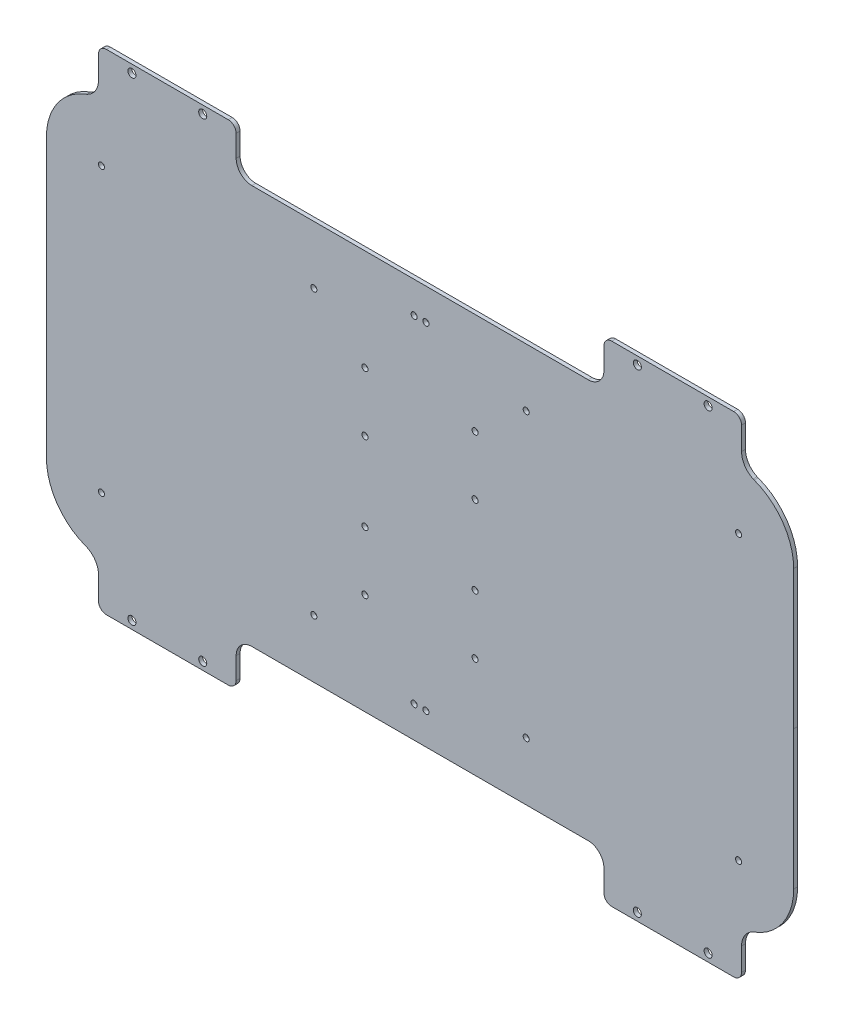
SolidWorks part; units mm, degrees
material "Thornel Mat VMA"
ref_plane "Front Plane" through (0, 0, 0) normal (0, 0, 1) x (1, 0, 0)
ref_plane "Top Plane" through (0, 0, 0) normal (0, 1, 0) x (1, 0, 0)
ref_plane "Right Plane" through (0, 0, 0) normal (1, 0, 0) x (0, 0, -1)
sketch "Sketch1" plane through (0, 0, 0) normal (0, 0, 1) x (1, 0, 0)
  line L0 (-89.5, -124.5) -> (-89.5, -101.5)
  line L1 (0, 0) -> (-188.8511, 0) construction
  line L2 (0, 0) -> (0, -155.176) construction
  line L4 (-167.5, -124.5) -> (-89.5, -124.5)
  line L15 (-167.5, -124.5) -> (-167.5, 124.5)
  line L16 (0, -153.8218) -> (0, 153.8218) construction
  line L17 (0, 0) -> (239.2725, 0) construction
  line L18 (-89.5, -113) -> (-167.5, -113) construction
  line L23 (-128.5, -113) -> (-128.5, -112.4029) construction
  line L24 (-146.5, -120.5) -> (-110.5, -120.5) construction
  line L29 (-128.5, -120.5) -> (-128.5, -79.0973) construction
  line L30 (128.5, -120.5) -> (128.5, -79.0973) construction
  line L35 (146.5, -120.5) -> (110.5, -120.5) construction
  line L36 (128.5, -113) -> (128.5, -112.4029) construction
  line L41 (89.5, -113) -> (167.5, -113) construction
  line L42 (167.5, -124.5) -> (167.5, 124.5)
  line L49 (167.5, -124.5) -> (89.5, -124.5)
  line L72 (89.5, -124.5) -> (89.5, -101.5)
  line L77 (89.5, 113) -> (167.5, 113) construction
  line L83 (128.5, 113) -> (128.5, 112.4029) construction
  line L84 (146.5, 120.5) -> (110.5, 120.5) construction
  line L89 (128.5, 120.5) -> (128.5, 79.0973) construction
  line L90 (-128.5, 120.5) -> (-128.5, 79.0973) construction
  line L95 (-146.5, 120.5) -> (-110.5, 120.5) construction
  line L96 (-128.5, 113) -> (-128.5, 112.4029) construction
  line L101 (-89.5, 113) -> (-167.5, 113) construction
  line L102 (89.5, 101.5) -> (-89.5, 101.5)
  line L108 (89.5, -101.5) -> (-89.5, -101.5)
  line L109 (89.5, 124.5) -> (89.5, 101.5)
  line L110 (167.5, 124.5) -> (89.5, 124.5)
  line L113 (-167.5, 124.5) -> (-89.5, 124.5)
  line L114 (-89.5, 124.5) -> (-89.5, 101.5)
  circle A2 centre (-146.5, -120.5) radius 2.05
  circle A3 centre (-110.5, -120.5) radius 2.05
  circle A4 centre (146.5, -120.5) radius 2.05
  circle A5 centre (110.5, -120.5) radius 2.05
  circle A42 centre (110.5, -120.5) radius 2.05
  circle A43 centre (146.5, -120.5) radius 2.05
  circle A44 centre (146.5, 120.5) radius 2.05
  circle A45 centre (110.5, 120.5) radius 2.05
  circle A48 centre (110.5, 120.5) radius 2.05
  circle A49 centre (146.5, 120.5) radius 2.05
  circle A50 centre (-110.5, 120.5) radius 2.05
  circle A51 centre (-146.5, 120.5) radius 2.05
  circle A52 centre (-28, -50) radius 1.55
  circle A53 centre (-28, -20) radius 1.55
  circle A54 centre (-28, 20) radius 1.55
  circle A55 centre (-28, 50) radius 1.55
  circle A56 centre (28, 50) radius 1.55
  circle A57 centre (28, 20) radius 1.55
  circle A58 centre (28, -20) radius 1.55
  circle A59 centre (28, -50) radius 1.55
  circle A109 centre (-162, -72) radius 1.55
  circle A110 centre (-54, -72) radius 1.55
  circle A111 centre (-162, 72) radius 1.55
  circle A112 centre (-54, 72) radius 1.55
  circle A113 centre (162, 72) radius 1.55
  circle A114 centre (54, 72) radius 1.55
  circle A115 centre (162, -72) radius 1.55
  circle A116 centre (54, -72) radius 1.55
  point P24 (0, -101.5)
  point P69 (167.5, 0)
  point P70 (-167.5, 0)
  point P71 (0, 101.5)
  dimension "D6" = 4
  dimension "D10" = 108
  dimension "D16" = 3.1
  dimension "D4" = 36
  dimension "D5" = 4.1
  dimension "D7" = 78
  dimension "D9" = 54
  dimension "D11" = 72
  dimension "D14" = 30
  dimension "D15" = 40
  dimension "D17" = 56
  dimension "D2" = 3.1
  dimension "D1" = 249
  dimension "D3" = 23
  dimension "D8" = 335
extrude "Boss-Extrude1" add sketch "Sketch1" along normal blind 2
fillet "圆角1" radius 10 4 edges at (-89.5, 101.5, 1) (89.5, 101.5, 1) (89.5, -101.5, 1) (-89.5, -101.5, 1)
fillet "圆角2" radius 3 8 edges at (167.5, -124.5, 1) (167.5, 124.5, 1) (-167.5, -124.5, 1) (-167.5, 124.5, 1) (89.5, 124.5, 1) (-89.5, 124.5, 1) (89.5, -124.5, 1) (-89.5, -124.5, 1)
sketch "草图1" plane through (0, 0, 2) normal (0, 0, 1) x (1, 0, 0)
  line L1 (0, 0) -> (-225.2559, 0) construction
  line L2 (0, 0) -> (0, -150.0532) construction
  line L3 (-189.9974, 0) -> (-190, -70.5859)
  line L4 (-165.4164, -103.8012) -> (-165.4164, 0)
  line L5 (-165.4164, 103.8012) -> (-165.4164, 0)
  line L6 (-189.9974, 0) -> (-190, 70.5859)
  line L7 (189.9974, 0) -> (190, 70.5859)
  line L8 (165.4164, 103.8012) -> (165.4164, 0)
  line L9 (165.4164, -103.8012) -> (165.4164, 0)
  line L10 (189.9974, 0) -> (190, -70.5859)
  arc A2 (-190, 70.5859) -> (-169.9278, 99.5417) centre (-159.0801, 70.5871) cw
  arc A3 (-169.9278, -99.5417) -> (-165.4164, -103.8012) centre (-172.7345, -107.0332) cw
  arc A4 (-190, -70.5859) -> (-169.9278, -99.5417) centre (-159.0801, -70.5871) ccw
  arc A5 (-169.9278, 99.5417) -> (-165.4164, 103.8012) centre (-172.7345, 107.0332) ccw
  arc A6 (169.9278, 99.5417) -> (165.4164, 103.8012) centre (172.7345, 107.0332) cw
  arc A7 (190, -70.5859) -> (169.9278, -99.5417) centre (159.0801, -70.5871) cw
  arc A8 (169.9278, -99.5417) -> (165.4164, -103.8012) centre (172.7345, -107.0332) ccw
  arc A9 (190, 70.5859) -> (169.9278, 99.5417) centre (159.0801, 70.5871) ccw
  dimension "D1" = 8
extrude "凸台-拉伸1" add sketch "草图1" against normal up to surface (2 mm away) contours L7 A9 A6 L8 L9 A8 A7 L10 | L5 L4 A3 A4 L3 L6 A2 A5 up to face at (163.55, -72, 0)
sketch "草图2" plane through (0, 0, 0) normal (0, 0, -1) x (-1, 0, 0)
  line L0 (-163.5, 108.8821) -> (-163.5, 125.1276)
  line L2 (-110.5, 120.5) -> (-146.5, 120.5) construction
  line L4 (-128.5, 120.5) -> (-128.5, 139.8938) construction
  line L5 (-163.5, 125.1276) -> (-195.49, 125.1276)
  line L6 (-195.49, 125.1276) -> (-190, 70.5859)
  line L7 (-60.8067, 101.5) -> (-85.5, 101.5)
  line L8 (-79.5, 101.5) -> (79.5, 101.5) construction
  line L9 (-93.5, 109.5) -> (-93.5, 125.1276)
  line L10 (-93.5, 125.1276) -> (-60.8067, 125.1276)
  line L11 (-60.8067, 125.1276) -> (-60.8067, 101.5)
  line L12 (0, 0) -> (0, -176.2697) construction
  line L13 (0, 0) -> (232.0428, 0) construction
  line L14 (128.5, 120.5) -> (128.5, 139.8938) construction
  line L15 (110.5, 120.5) -> (146.5, 120.5) construction
  line L16 (60.8067, 125.1276) -> (60.8067, 101.5)
  line L17 (93.5, 125.1276) -> (60.8067, 125.1276)
  line L18 (93.5, 109.5) -> (93.5, 125.1276)
  line L19 (60.8067, 101.5) -> (85.5, 101.5)
  line L20 (195.49, 125.1276) -> (190, 70.5859)
  line L21 (163.5, 125.1276) -> (195.49, 125.1276)
  line L22 (163.5, 108.8821) -> (163.5, 125.1276)
  line L23 (110.5, -120.5) -> (146.5, -120.5) construction
  line L24 (128.5, -120.5) -> (128.5, -139.8938) construction
  line L25 (-128.5, -120.5) -> (-128.5, -139.8938) construction
  line L26 (-110.5, -120.5) -> (-146.5, -120.5) construction
  line L27 (163.5, -108.8821) -> (163.5, -125.1276)
  line L28 (163.5, -125.1276) -> (195.49, -125.1276)
  line L29 (195.49, -125.1276) -> (190, -70.5859)
  line L30 (60.8067, -101.5) -> (85.5, -101.5)
  line L31 (93.5, -109.5) -> (93.5, -125.1276)
  line L32 (93.5, -125.1276) -> (60.8067, -125.1276)
  line L33 (60.8067, -125.1276) -> (60.8067, -101.5)
  line L34 (-60.8067, -125.1276) -> (-60.8067, -101.5)
  line L35 (-93.5, -125.1276) -> (-60.8067, -125.1276)
  line L36 (-93.5, -109.5) -> (-93.5, -125.1276)
  line L37 (-60.8067, -101.5) -> (-85.5, -101.5)
  line L38 (-195.49, -125.1276) -> (-190, -70.5859)
  line L39 (-163.5, -125.1276) -> (-195.49, -125.1276)
  line L40 (-163.5, -108.8821) -> (-163.5, -125.1276)
  arc A0 (-169.9278, 99.5417) -> (-190, 70.5859) centre (-159.0801, 70.5871) ccw construction
  arc A1 (-169.9761, 99.5235) -> (-190, 70.5859) centre (-159.0801, 70.5871) ccw
  arc A2 (-169.9761, 99.5235) -> (-163.5, 108.8821) centre (-173.5, 108.8821) ccw
  arc A3 (-85.5, 101.5) -> (-93.5, 109.5) centre (-85.5, 109.5) cw
  arc A4 (85.5, 101.5) -> (93.5, 109.5) centre (85.5, 109.5) ccw
  arc A5 (169.9761, 99.5235) -> (163.5, 108.8821) centre (173.5, 108.8821) cw
  arc A6 (169.9761, 99.5235) -> (190, 70.5859) centre (159.0801, 70.5871) cw
  arc A7 (169.9761, -99.5235) -> (190, -70.5859) centre (159.0801, -70.5871) ccw
  arc A8 (169.9761, -99.5235) -> (163.5, -108.8821) centre (173.5, -108.8821) ccw
  arc A9 (85.5, -101.5) -> (93.5, -109.5) centre (85.5, -109.5) cw
  arc A10 (-85.5, -101.5) -> (-93.5, -109.5) centre (-85.5, -109.5) ccw
  arc A11 (-169.9761, -99.5235) -> (-163.5, -108.8821) centre (-173.5, -108.8821) cw
  arc A12 (-169.9761, -99.5235) -> (-190, -70.5859) centre (-159.0801, -70.5871) cw
  dimension "D2" = 10
  dimension "D3" = 8
  dimension "D1" = 35
extrude "切除-拉伸1" cut sketch "草图2" against normal blind 10
fillet "圆角3" radius 4 8 edges at (-93.5, 124.5, 1) (-163.5, 124.5, 1) (93.5, 124.5, 1) (163.5, 124.5, 1) (163.5, -124.5, 1) (93.5, -124.5, 1) (-93.5, -124.5, 1) (-163.5, -124.5, 1)
sketch "Sketch2" plane through (0, 0, 0) normal (0, 0, -1) x (-1, 0, 0)
  line L0 (-22.86, 27.4315) -> (22.86, 27.4332) construction
  line L2 (0, 27.4324) -> (0, -47.4376) construction
  line L3 (0, -47.4376) -> (-24.13, -47.4376) construction
  line L4 (-24.13, -47.4376) -> (-24.13, -48.7376) construction
  line L5 (-24.13, -48.7376) -> (24.13, -48.7376) construction
  circle A0 centre (22.86, 27.4332) radius 1.55
  circle A1 centre (-22.86, 27.4315) radius 1.55
  circle A2 centre (-24.13, -47.4376) radius 1.55
  circle A3 centre (24.13, -48.7376) radius 1.55
  circle A4 centre (1.21, 13.4615) radius 1.55
  point P0 (0, -10.0026)
  point P3 (0, 27.4324)
  dimension "D1" = 3.1
  dimension "D2" = 45.72
  dimension "D3" = 74.87
  dimension "D4" = 24.13
  dimension "D5" = 1.3
  dimension "D6" = 48.26
  dimension "D7" = 24.07
  dimension "D8" = 13.97
  dimension "D9" = 10.0026
sketch "Sketch3" plane through (0, 0, 0) normal (0, 0, -1) x (-1, 0, 0)
  line L1 (-82, -52.5) -> (-82, 52.5) construction
  line L2 (-82, -52.5) -> (-58, -52.5) construction
  line L3 (-58, -52.5) -> (-58, 52.5) construction
  line L4 (-82, 52.5) -> (-58, 52.5) construction
  line L5 (-82, -52.5) -> (-58, 52.5) construction
  line L6 (-58, -52.5) -> (-82, 52.5) construction
  circle A0 centre (-58, 52.5) radius 1.55
  circle A1 centre (-82, 52.5) radius 1.55
  circle A2 centre (-58, -52.5) radius 1.55
  circle A3 centre (-82, -52.5) radius 1.55
  point P0 (-70, 0)
  dimension "D1" = 3.1
  dimension "D2" = 105
  dimension "D3" = 24
  dimension "D4" = 70
sketch "Sketch4" plane through (0, 0, 0) normal (0, 0, -1) x (-1, 0, 0)
  line L0 (190, -70.5859) -> (189.9974, 0) construction
  line L1 (51.9974, 36) -> (87.9974, 36) construction
  line L2 (51.9974, 36) -> (51.9974, -36) construction
  line L3 (51.9974, -36) -> (87.9974, -36) construction
  line L4 (87.9974, 36) -> (87.9974, -36) construction
  line L5 (51.9974, 36) -> (87.9974, -36) construction
  line L6 (51.9974, -36) -> (87.9974, 36) construction
  circle A0 centre (51.9974, -36) radius 1.55
  circle A1 centre (87.9974, -36) radius 1.55
  circle A2 centre (87.9974, 36) radius 1.55
  circle A3 centre (51.9974, 36) radius 1.55
  point P0 (69.9974, 0)
  dimension "D3" = 3.1
  dimension "D1" = 72
  dimension "D2" = 36
  dimension "D4" = 120
sketch "Sketch5" plane through (0, 0, 0) normal (0, 0, -1) x (-1, 0, 0)
  line L1 (6, 88) -> (-6, 88) construction
  line L2 (6, 88) -> (6, 83) construction
  line L3 (6, 83) -> (-6, 83) construction
  line L4 (-6, 88) -> (-6, 83) construction
  line L5 (6, 85.5) -> (-6, 85.5) construction
  line L6 (0, 83) -> (0, 90.0158) construction
  line L7 (15.3877, 0) -> (-26.8414, 0) construction
  line L8 (-85.5, 101.5) -> (85.5, 101.5) construction
  circle A0 centre (3, 85.5) radius 1.55
  circle A1 centre (-3, 85.5) radius 1.55
  circle A2 centre (-3, -85.5) radius 1.55
  circle A3 centre (3, -85.5) radius 1.55
  dimension "D1" = 5
  dimension "D4" = 3.1
  dimension "D5" = 3.1
  dimension "D2" = 12
  dimension "D3" = 6
  dimension "D6" = 6
  dimension "D7" = 3
  dimension "D8" = 16
extrude "Cut-Extrude1" cut sketch "Sketch5" against normal blind 10
